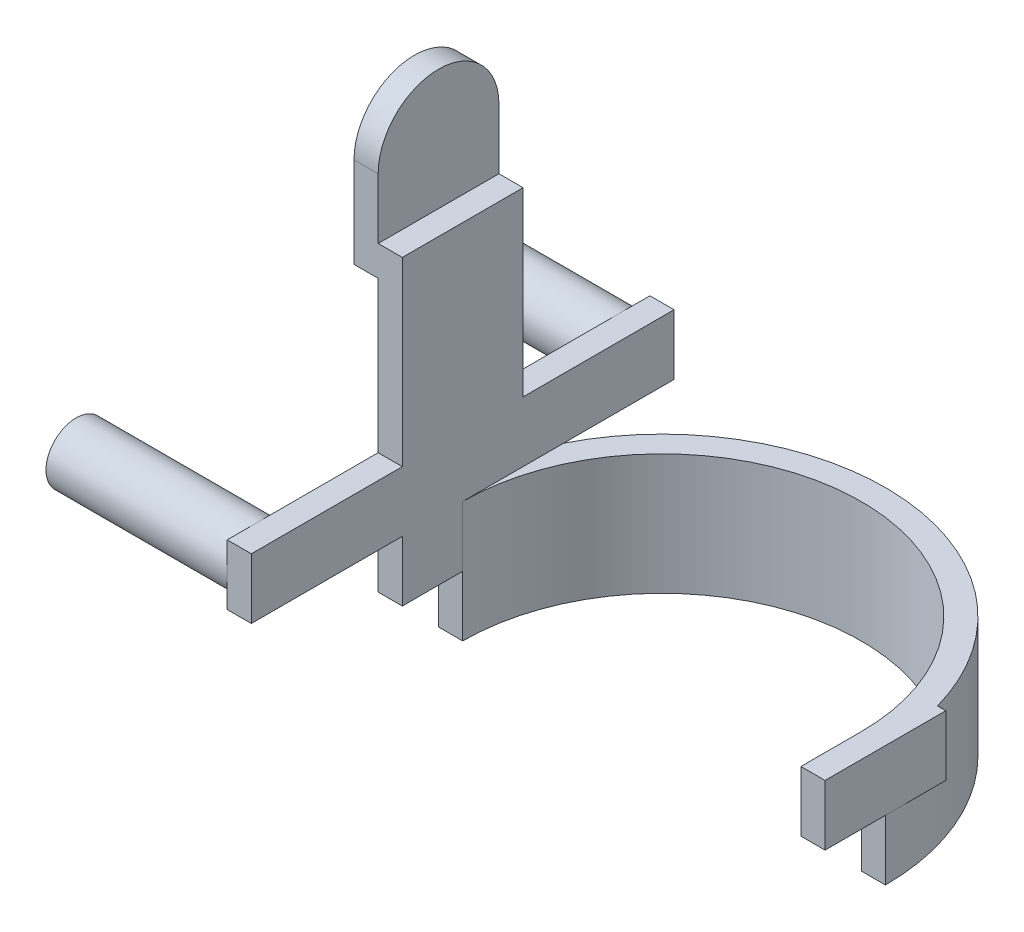
SolidWorks part; units mm, degrees
ref_plane "Front" through (0, 0, 0) normal (0, 0, 1) x (1, 0, 0)
ref_plane "Top" through (0, 0, 0) normal (0, 1, 0) x (1, 0, 0)
ref_plane "Right" through (0, 0, 0) normal (1, 0, 0) x (0, 0, -1)
sketch "草图1" plane through (0, 0, 0) normal (0, 1, 0) x (1, 0, 0)
  line L0 (-72.3418, 0) -> (74, 0) construction
  line L1 (0, 74) -> (0, -74) construction
  line L3 (-74, 20) -> (-71.2461, 20)
  line L4 (-74, 20) -> (-74, -20)
  line L5 (-74, -20) -> (-66, -20)
  line L6 (-66, 0) -> (-66, -20)
  line L7 (74, 20) -> (71.2461, 20)
  line L8 (74, 20) -> (74, -20)
  line L9 (74, -20) -> (66, -20)
  line L10 (66, 0) -> (66, -20)
  arc A0 (71.2461, 20) -> (-71.2461, 20) centre (0, 0) ccw
  arc A1 (66, 0) -> (-66, 0) centre (0, 0) ccw
  dimension "D1" = 40
  dimension "D2" = 20
  dimension "D3" = 8
  dimension "D4" = 8
  dimension "D6" = 40
  dimension "D7" = 20
extrude "凸台-拉伸1" add sketch "草图1" along normal blind 40
sketch "草图2" plane through (0, 40, 0) normal (0, 1, 0) x (1, 0, 0)
  line L1 (-74, -20) -> (-66, -20)
  line L2 (-74, -20) -> (-74, 20)
  line L3 (-74, 20) -> (-66, 20)
  line L4 (-66, -20) -> (-66, 20)
  line L5 (66, -20) -> (74, -20)
  line L6 (66, -20) -> (66, 20)
  line L7 (66, 20) -> (74, 20)
  line L8 (74, -20) -> (74, 20)
  dimension "D1" = 8
extrude "凸台-拉伸2" add sketch "草图2" along normal blind 80
sketch "草图5" plane through (74, 0, 0) normal (1, 0, 0) x (0, 0, -1)
  line L1 (20, 40) -> (-67.0077, 40)
  line L2 (20, 40) -> (20, 155.015)
  line L3 (20, 155.015) -> (-67.0077, 155.015)
  line L4 (-67.0077, 40) -> (-67.0077, 155.015)
extrude "切除-拉伸2" cut sketch "草图5" against normal blind 10
sketch "草图6" plane through (0, 0, 0) normal (0, -1, 0) x (1, 0, 0)
  line L1 (-71.2461, 20) -> (-66, 20)
  line L3 (-74, 0) -> (-66, 0)
  line L4 (-66, 20) -> (-66, 0)
  line L5 (71.2461, 20) -> (66, 20)
  line L7 (74, 0) -> (66, 0)
  line L8 (66, 20) -> (66, 0)
  arc A0 (-74, 0) -> (74, 0) centre (0, 0) ccw
  circle A1 centre (0, 0) radius 85.0634
  arc A2 (71.2461, 20) -> (-71.2461, 20) centre (0, 0) ccw
extrude "切除-拉伸3" cut sketch "草图6" against normal blind 20
sketch "草图7" plane through (-74, 0, 0) normal (-1, 0, 0) x (0, 0, 1)
  line L0 (0, 0) -> (0, 85.622) construction
  line L1 (-70, 60) -> (70, 60)
  line L2 (-70, 60) -> (-70, 40)
  line L3 (-70, 40) -> (70, 40)
  line L4 (70, 60) -> (70, 40)
  dimension "D1" = 40
  dimension "D2" = 140
  dimension "D3" = 70
  dimension "D4" = 20
extrude "凸台-拉伸3" add sketch "草图7" against normal blind 8
sketch "草图9" plane through (-74, 0, 0) normal (-1, 0, 0) x (0, 0, 1)
  circle A0 centre (-60, 50) radius 10
  circle A1 centre (60, 50) radius 10
extrude "凸台-拉伸4" add sketch "草图9" along normal blind 60
sketch "草图10" plane through (0, 0, 20) normal (0, 0, 1) x (1, 0, 0)
  line L0 (-74, 120) -> (-74, 60) construction
  line L1 (-74, 110) -> (-82, 110)
  line L2 (-74, 110) -> (-74, 160)
  line L3 (-74, 160) -> (-82, 160)
  line L4 (-82, 110) -> (-82, 160)
  line L5 (-74, 120) -> (-66, 120) construction
  dimension "D1" = 8
  dimension "D2" = 50
  dimension "D3" = 10
extrude "凸台-拉伸5" add sketch "草图10" against normal blind 40
sketch "草图11" plane through (-82, 0, 0) normal (-1, 0, 0) x (0, 0, 1)
  line L2 (-20, 140) -> (-20, 168.2585)
  line L3 (-20, 168.2585) -> (20, 168.2585)
  line L4 (20, 140) -> (20, 168.2585)
  arc A0 (20, 140) -> (-20, 140) centre (0, 140) ccw
extrude "切除-拉伸4" cut sketch "草图11" against normal blind 40
